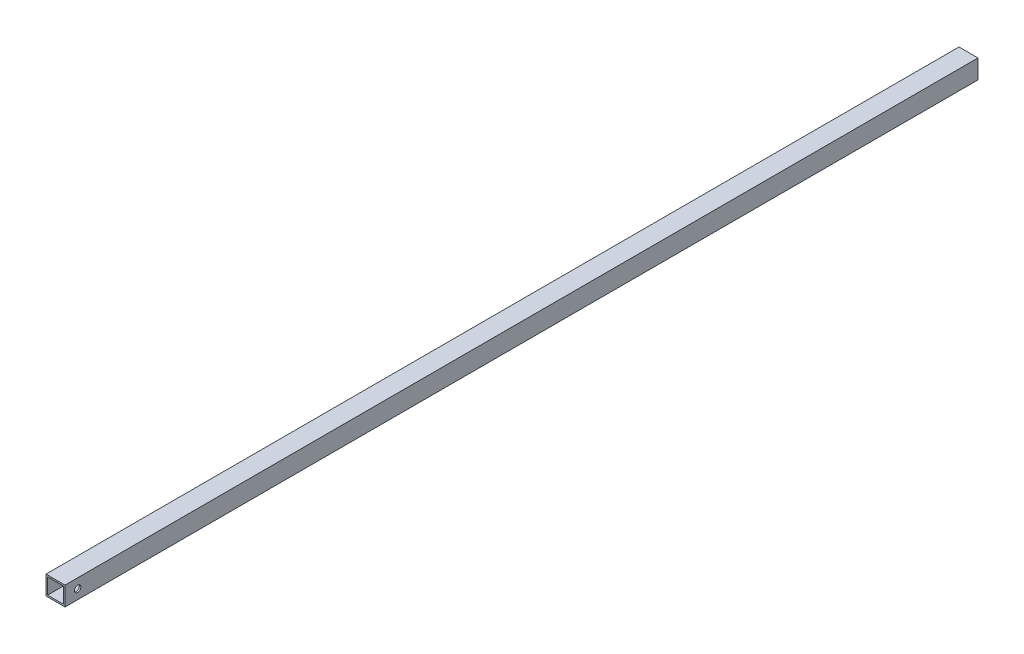
SolidWorks part; units mm, degrees
material "6061-T6 (SS)"
ref_plane "Front Plane" through (0, 0, 0) normal (0, 0, 1) x (1, 0, 0)
ref_plane "Top Plane" through (0, 0, 0) normal (0, 1, 0) x (1, 0, 0)
ref_plane "Right Plane" through (0, 0, 0) normal (1, 0, 0) x (0, 0, -1)
sketch "Sketch1" plane through (0, 0, 0) normal (0, 0, 1) x (1, 0, 0)
  line L0 (-15.875, 15.875) -> (-15.875, -15.875)
  line L1 (-19.05, 19.05) -> (19.05, 19.05)
  line L2 (-19.05, 19.05) -> (-19.05, -19.05)
  line L3 (-19.05, -19.05) -> (19.05, -19.05)
  line L4 (19.05, 19.05) -> (19.05, -19.05)
  line L5 (-19.05, 19.05) -> (19.05, -19.05) construction
  line L6 (-19.05, -19.05) -> (19.05, 19.05) construction
  line L7 (-15.875, -15.875) -> (15.875, -15.875)
  line L8 (15.875, 15.875) -> (15.875, -15.875)
  line L9 (-15.875, 15.875) -> (15.875, 15.875)
  point P0 (0, 0)
  dimension "D1" = 38.1
  dimension "D2" = 38.1
  dimension "D3" = 3.175
extrude "Boss-Extrude1" add sketch "Sketch1" against normal blind 1828.8
sketch "Sketch2" plane through (-19.05, 0, 0) normal (-1, 0, 0) x (0, 0, 1)
  line L0 (0, 19.05) -> (0, -19.05) construction
  circle A0 centre (-25.4, 0) radius 6.35
  dimension "D1" = 12.7
  dimension "D2" = 25.4
extrude "Cut-Extrude1" cut sketch "Sketch2" against normal up to surface (38.1 mm away) up to face at (19.05, 0, -914.4)
